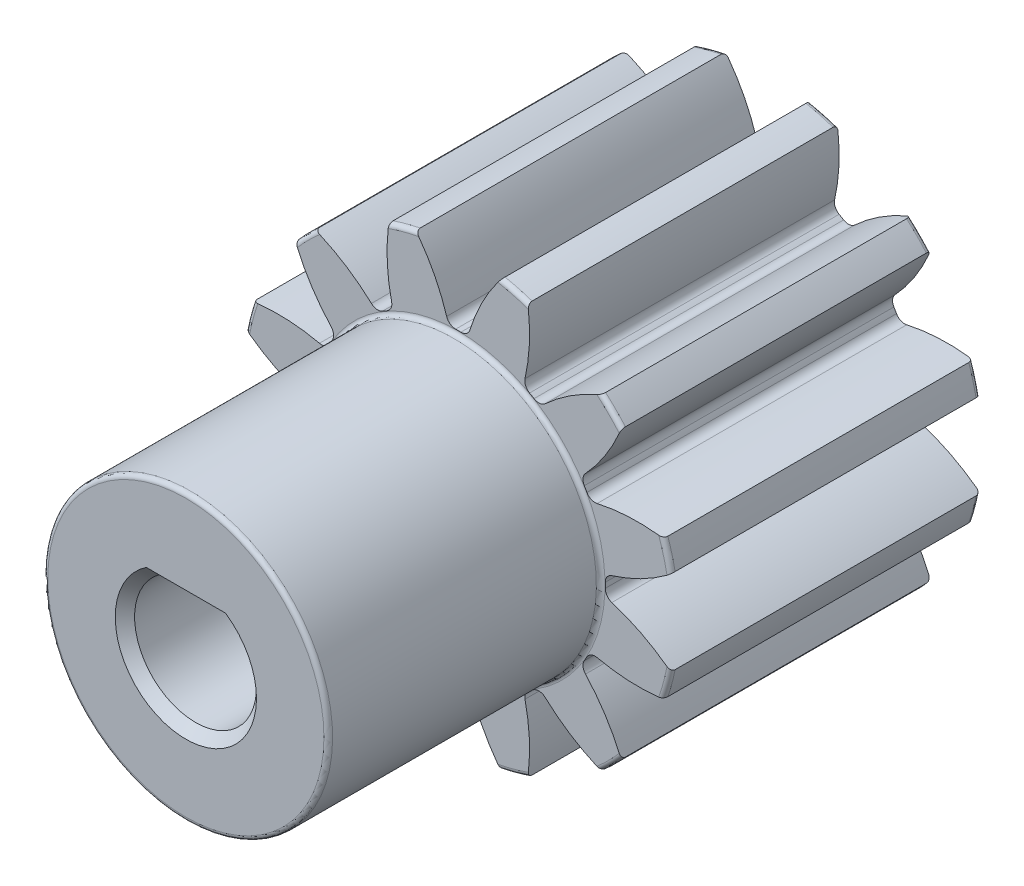
SolidWorks part; units mm, degrees
ref_plane "Front Plane" through (0, 0, 0) normal (0, 0, 1) x (1, 0, 0)
ref_plane "Top Plane" through (0, 0, 0) normal (0, 1, 0) x (1, 0, 0)
ref_plane "Right Plane" through (0, 0, 0) normal (1, 0, 0) x (0, 0, -1)
sketch "Sketch1" plane through (0, 0, 0) normal (0, 0, 1) x (1, 0, 0)
  line L0 (-152.4, 0) -> (152.4, 0) construction
  circle A0 centre (0, 0) radius 8.89 construction
  circle A1 centre (0, 0) radius 7.62 construction
  circle A2 centre (0, 0) radius 6.0325 construction
  circle A3 centre (0, 0) radius 5.842 construction
  circle A4 centre (0, 0) radius 2.5 construction
  dimension "D2" = 1.27
  dimension "D3" = 2.8575
  dimension "D1" = 2.8575
sketch "Sketch2" plane through (0, 0, 0) normal (1, 0, 0) x (0, 0, -1)
  line L0 (0, 0) -> (-12.7, 0) construction
  line L1 (-12.7, 0) -> (-23.876, 0) construction
  dimension "Overall Width" = 23.876
  dimension "Face Width" = 12.7
sketch "Sketch4" plane through (0, 0, 0) normal (1, 0, 0) x (0, 0, -1)
  line L0 (-23.876, 2.5) -> (-23.876, 5.842)
  line L1 (-23.876, 5.842) -> (-12.7, 5.842)
  line L2 (-12.7, 5.842) -> (-12.7, 8.89)
  line L3 (-12.7, 8.89) -> (0, 8.89)
  line L4 (0, 8.89) -> (0, 2.5)
  line L5 (-12.7, 5.842) -> (-12.7, 0) construction
  line L6 (0, 8.89) -> (0, -8.89) construction
  line L7 (-12.7, 5.842) -> (0, 5.842) construction
  line L12 (-23.876, 2.5) -> (0, 2.5)
revolve "Revolve1" add sketch "Sketch4" angle 360 about L1
fillet "Fillet2" radius 0.1778 4 edges at (0, 5.842, 23.876) (0, 5.842, 12.7) (0, 8.89, 12.7) (0, 8.89, 0)
sketch "Sketch7" plane through (0, 0, 12.7) normal (0, 0, 1) x (1, 0, 0)
  line L0 (0, 0) -> (0, 8.89) construction
  line L1 (0.9946, 7.5548) -> (1.6129, 8.7425) construction
  line L3 (2.3009, 8.5871) -> (1.9722, 7.3604) construction
  line L4 (1.9722, 7.3604) -> (1.5613, 5.8269) construction
  line L5 (0, 0) -> (1.5613, 5.8269) construction
  line L6 (0.9946, 7.5548) -> (0, 0) construction
  line L7 (0.9946, 7.5548) -> (1.1604, 8.8139) construction
  line L8 (0.9946, 7.5548) -> (0, 0) construction
  circle A0 centre (0, 0) radius 8.89 construction
  arc A1 (-0.1069, 6.0316) -> (0.1069, 6.0316) centre (0, 0) cw
  circle A2 centre (0, 0) radius 6.0325 construction
  arc A3 (-0.9946, 7.5548) -> (0.9946, 7.5548) centre (0, 0) cw construction
  circle A4 centre (0, 0) radius 7.62 construction
  arc A5 (2.8509, 8.4205) -> (1.7413, 8.7178) centre (0, 0) ccw construction
  arc A6 (0.9946, 7.5548) -> (2.916, 7.04) centre (0, 0) cw construction
  arc A7 (-1.7413, 8.7178) -> (1.7413, 8.7178) centre (0, 0) cw
  arc A8 (0.4774, 6.2994) -> (1.7413, 8.7178) centre (7.7536, 4.0363) cw
  arc A9 (-0.4774, 6.2994) -> (-1.7413, 8.7178) centre (-7.7536, 4.0363) ccw
  arc A10 (-0.1069, 6.0316) -> (-0.4774, 6.2994) centre (-0.1136, 6.4125) cw
  arc A11 (0.1069, 6.0316) -> (0.4774, 6.2994) centre (0.1136, 6.4125) ccw
  point P26 (-0.3962, 6.0195)
  point P29 (0.3962, 6.0195)
  dimension "D4" = 0.381
  dimension "D5" = 7.62
  dimension "D3" = 20
  dimension "D1" = 3.9898
  dimension "D2" = 1.9949
extrude "Cut-Extrude2" cut sketch "Sketch7" against normal through all
pattern_circular "CirPattern1" count 12 over 360 about axis through (0, 0, 0) along (0, 0, 1) of "Cut-Extrude2"
sketch "Sketch8" plane through (0, 0, 0) normal (0, 0, -1) x (-1, 0, 0)
  line L0 (-1.5, 2) -> (1.5, 2)
  circle A0 centre (0, 0) radius 2.5 construction
  arc A1 (1.5, 2) -> (-1.5, 2) centre (0, 0) ccw
  point P0 (0, 2.5)
  point P5 (-0.692, 2.4023)
  dimension "D1" = 0.5
extrude "Boss-Extrude1" add sketch "Sketch8" against normal up to surface (23.876 mm away) up to face at (0, -5.6642, 23.876)
chamfer "Chamfer1" distance 0.3969 angle 45 4 edges at (0, -2.5, 23.876) (0, 2, 23.876) (0, 2, 0) (0, -2.5, 0)
equation "\"D1@Sketch1\"=2.25*(\"Pitch Dia.@Sketch1\"/\"Number of Teeth@Sketch1\")"
equation "\"D1@CirPattern1\"=\"Number of Teeth@Sketch1\""
equation "\"D1@Fillet2\"=\"OD@Sketch1\"*.01"
equation "\"D1@Sketch7\"=3.14159*(\"Pitch Dia.@Sketch1\"/\"Number of Teeth@Sketch1\")"
equation "\"D2@Sketch7\"=\"D1@Sketch7\"/2"
equation "\"D4@Sketch7\"=\"D1@Sketch7\"*.0955"
equation "\"D5@Sketch7\"=\"Pitch Dia.@Sketch1\"/2"
